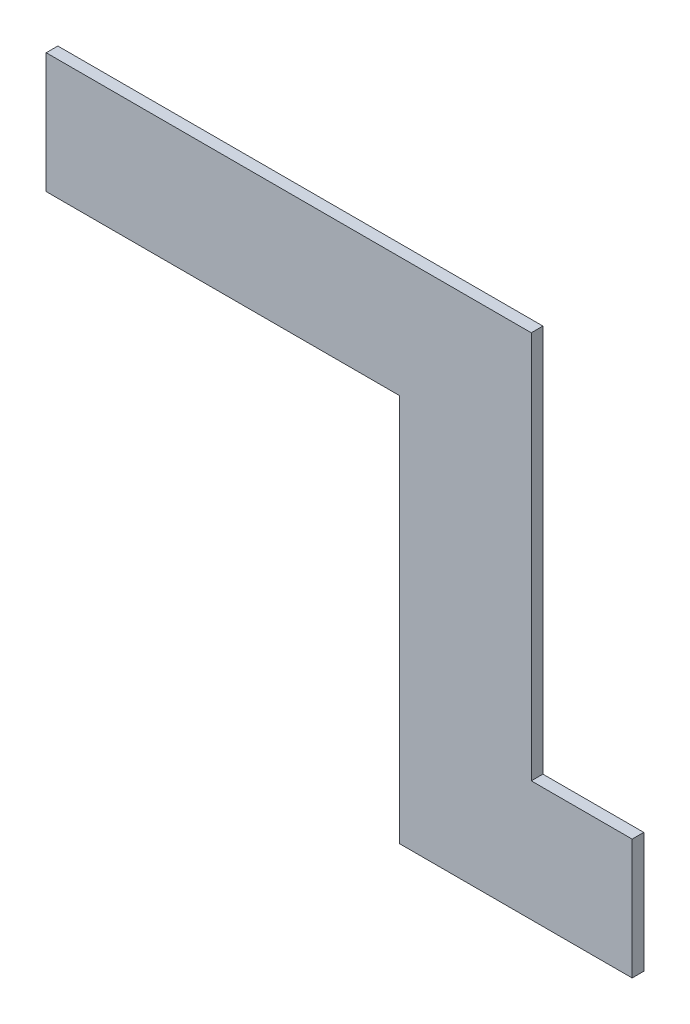
SolidWorks part; units mm, degrees
ref_plane "Plan de face" through (0, 0, 0) normal (0, 0, 1) x (1, 0, 0)
ref_plane "Plan de dessus" through (0, 0, 0) normal (0, 1, 0) x (1, 0, 0)
ref_plane "Plan de droite" through (0, 0, 0) normal (1, 0, 0) x (0, 0, -1)
sketch "Esquisse1" plane through (0, 0, 0) normal (0, 0, 1) x (1, 0, 0)
  line L0 (-91, 81) -> (-91, 50)
  line L1 (-91, 50) -> (0, 50)
  line L2 (0, 50) -> (0, -50)
  line L3 (0, -50) -> (60, -50)
  line L4 (60, -50) -> (60, -19)
  line L5 (60, -19) -> (34, -19)
  line L6 (34, -19) -> (34, 81)
  line L7 (34, 81) -> (-91, 81)
  point P7 (0, 0)
  dimension "D1" = 31
  dimension "D2" = 31
  dimension "D3" = 125
  dimension "D4" = 100
  dimension "D5" = 26
  dimension "D6" = 34
extrude "Boss.-Extru.1" add sketch "Esquisse1" along normal blind 3
